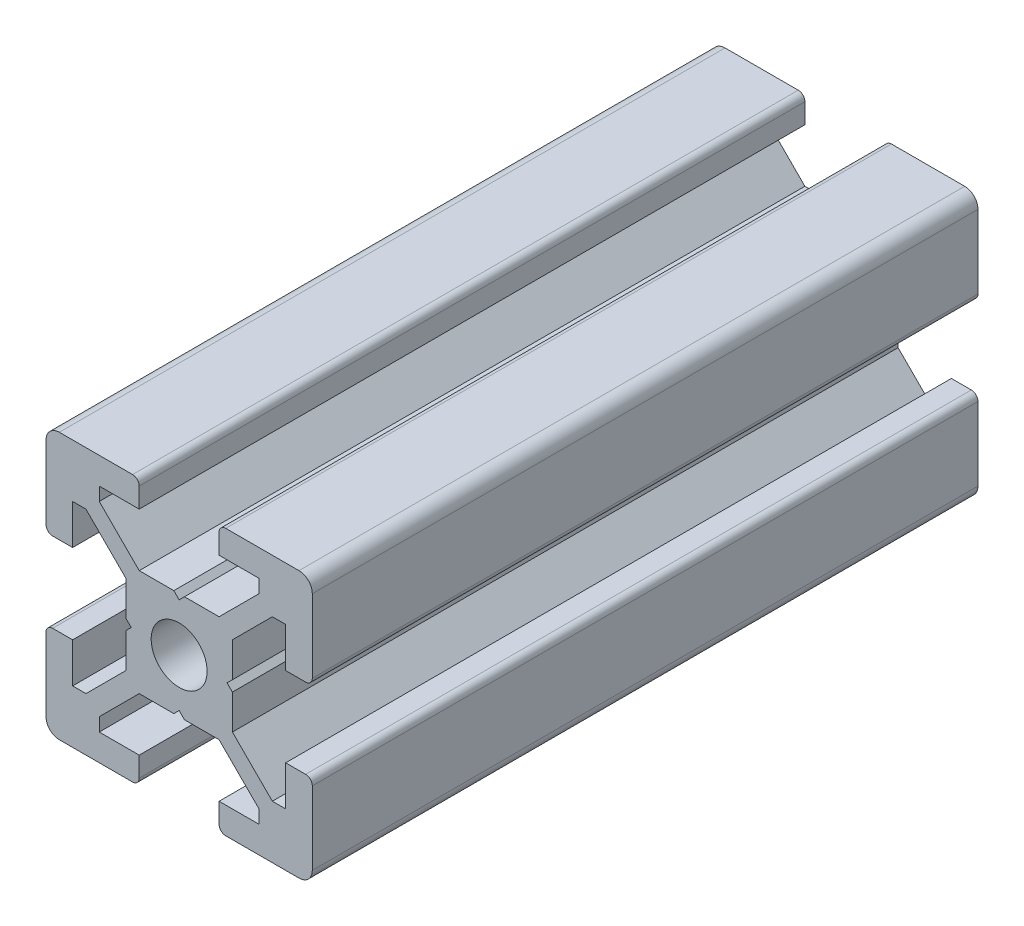
SolidWorks part; units mm, degrees
material "Lega 6061"
ref_plane "Piano frontale" through (0, 0, 0) normal (0, 0, 1) x (1, 0, 0)
ref_plane "Piano superiore" through (0, 0, 0) normal (0, 1, 0) x (1, 0, 0)
ref_plane "Piano destro" through (0, 0, 0) normal (1, 0, 0) x (0, 0, -1)
sketch "Schizzo1" plane through (0, 0, 0) normal (0, 0, 1) x (1, 0, 0)
  line L0 (0, 0) -> (-10, 0) construction
  line L1 (0, 0) -> (0, 10) construction
  line L2 (-3.6, 0) -> (-4, 0.4)
  line L3 (-4, 0.4) -> (-4, 3)
  line L4 (-4, 3) -> (-7, 6)
  line L5 (-7, 6) -> (-8, 6)
  line L6 (-8, 6) -> (-8, 3)
  line L7 (-8, 3) -> (-9.5, 3)
  line L8 (-10, 3.5) -> (-10, 9)
  line L9 (0, 0) -> (-10, 10) construction
  line L10 (0, 3.6) -> (-0.4, 4)
  line L11 (-0.4, 4) -> (-3, 4)
  line L12 (-3, 4) -> (-6, 7)
  line L13 (-6, 7) -> (-6, 8)
  line L14 (-6, 8) -> (-3, 8)
  line L15 (-3, 8) -> (-3, 9.5)
  line L16 (-3.5, 10) -> (-9, 10)
  line L17 (0, 0) -> (-10, -10) construction
  line L18 (-3.5, -10) -> (-9, -10)
  line L19 (-3, -8) -> (-3, -9.5)
  line L20 (-6, -8) -> (-3, -8)
  line L21 (-6, -7) -> (-6, -8)
  line L22 (-3, -4) -> (-6, -7)
  line L23 (-0.4, -4) -> (-3, -4)
  line L24 (0, -3.6) -> (-0.4, -4)
  line L25 (-10, -3.5) -> (-10, -9)
  line L26 (-8, -3) -> (-9.5, -3)
  line L27 (-8, -6) -> (-8, -3)
  line L28 (-7, -6) -> (-8, -6)
  line L29 (-4, -3) -> (-7, -6)
  line L30 (-4, -0.4) -> (-4, -3)
  line L31 (-3.6, 0) -> (-4, -0.4)
  line L32 (0, 0) -> (10, -10) construction
  line L33 (0, 0) -> (10, 10) construction
  line L34 (3.6, 0) -> (4, -0.4)
  line L35 (4, -0.4) -> (4, -3)
  line L36 (4, -3) -> (7, -6)
  line L37 (7, -6) -> (8, -6)
  line L38 (8, -6) -> (8, -3)
  line L39 (8, -3) -> (9.5, -3)
  line L40 (10, -3.5) -> (10, -9)
  line L41 (0, -3.6) -> (0.4, -4)
  line L42 (0.4, -4) -> (3, -4)
  line L43 (3, -4) -> (6, -7)
  line L44 (6, -7) -> (6, -8)
  line L45 (6, -8) -> (3, -8)
  line L46 (3, -8) -> (3, -9.5)
  line L47 (3.5, -10) -> (9, -10)
  line L48 (3.5, 10) -> (9, 10)
  line L49 (3, 8) -> (3, 9.5)
  line L50 (6, 8) -> (3, 8)
  line L51 (6, 7) -> (6, 8)
  line L52 (3, 4) -> (6, 7)
  line L53 (0.4, 4) -> (3, 4)
  line L54 (0, 3.6) -> (0.4, 4)
  line L55 (10, 3.5) -> (10, 9)
  line L56 (8, 3) -> (9.5, 3)
  line L57 (8, 6) -> (8, 3)
  line L58 (7, 6) -> (8, 6)
  line L59 (4, 3) -> (7, 6)
  line L60 (4, 0.4) -> (4, 3)
  line L61 (3.6, 0) -> (4, 0.4)
  arc A0 (-10, 9) -> (-9, 10) centre (-9, 9) cw
  arc A1 (-3, 9.5) -> (-3.5, 10) centre (-3.5, 9.5) ccw
  arc A2 (-9.5, 3) -> (-10, 3.5) centre (-9.5, 3.5) cw
  arc A3 (-9.5, -3) -> (-10, -3.5) centre (-9.5, -3.5) ccw
  arc A4 (-3, -9.5) -> (-3.5, -10) centre (-3.5, -9.5) cw
  arc A5 (-10, -9) -> (-9, -10) centre (-9, -9) ccw
  arc A6 (10, -9) -> (9, -10) centre (9, -9) cw
  arc A7 (3, -9.5) -> (3.5, -10) centre (3.5, -9.5) ccw
  arc A8 (9.5, -3) -> (10, -3.5) centre (9.5, -3.5) cw
  arc A9 (9.5, 3) -> (10, 3.5) centre (9.5, 3.5) ccw
  arc A10 (3, 9.5) -> (3.5, 10) centre (3.5, 9.5) cw
  arc A11 (10, 9) -> (9, 10) centre (9, 9) ccw
  circle A12 centre (0, 0) radius 2.1
  point P24 (-3, 10)
  point P27 (-10, 3)
  point P49 (-10, -3)
  point P50 (-3, -10)
  point P92 (3, -10)
  point P93 (10, -3)
  point P94 (10, 3)
  point P95 (3, 10)
  dimension "D2" = 1
  dimension "D12" = 0.5
  dimension "D13" = 4.2
  dimension "D3" = 8
  dimension "D4" = 0.4
  dimension "D5" = 45
  dimension "D6" = 6
  dimension "D7" = 12
  dimension "D8" = 20
  dimension "D9" = 2
  dimension "D10" = 4
  dimension "D11" = 45
extrude "Estrusione-Estrusione1" add sketch "Schizzo1" along normal blind 50
